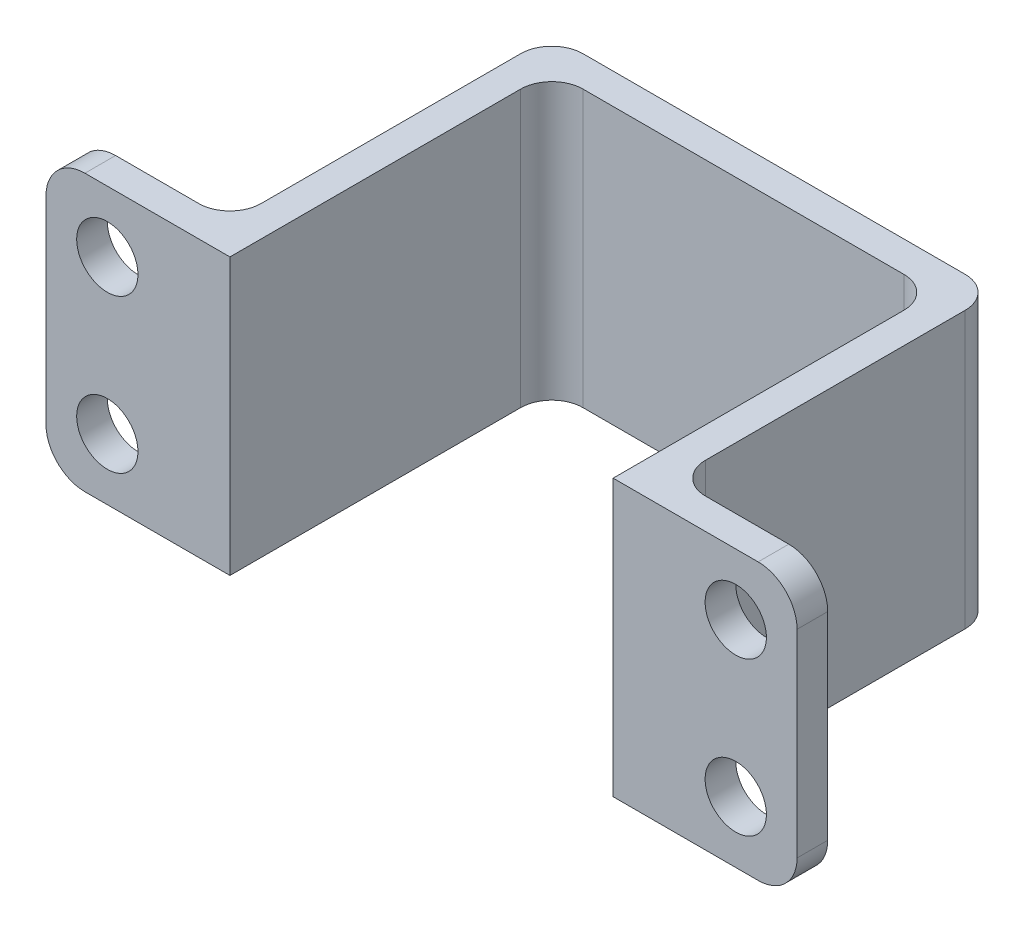
SolidWorks part; units mm, degrees
ref_plane "Front Plane" through (0, 0, 0) normal (0, 0, 1) x (1, 0, 0)
ref_plane "Top Plane" through (0, 0, 0) normal (0, 1, 0) x (1, 0, 0)
ref_plane "Right Plane" through (0, 0, 0) normal (1, 0, 0) x (0, 0, -1)
sketch "Sketch1" plane through (0, 0, 0) normal (0, 1, 0) x (1, 0, 0)
  line L0 (12.5, 0) -> (13.5, 0)
  line L2 (0, 0) -> (0, 9.484)
  line L3 (1.016, 10.5) -> (11.484, 10.5)
  line L4 (12.5, 0) -> (12.5, 9.484)
  line L5 (-1, 0) -> (0, 0)
  line L6 (-1, 2.016) -> (-1, 10.484)
  line L7 (0.016, 11.5) -> (12.484, 11.5)
  line L8 (13.5, 2.016) -> (13.5, 10.484)
  line L10 (-1, 0) -> (-6, 0)
  line L12 (-2.016, 1) -> (-6, 1)
  line L13 (-6, 0) -> (-6, 1)
  line L14 (13.5, 0) -> (18.5, 0)
  line L16 (14.516, 1) -> (18.5, 1)
  line L17 (18.5, 0) -> (18.5, 1)
  arc A0 (13.5, 2.016) -> (14.516, 1) centre (14.516, 2.016) ccw
  arc A1 (-1, 10.484) -> (0.016, 11.5) centre (0.016, 10.484) cw
  arc A2 (12.484, 11.5) -> (13.5, 10.484) centre (12.484, 10.484) cw
  arc A3 (11.484, 10.5) -> (12.5, 9.484) centre (11.484, 9.484) cw
  arc A4 (0, 9.484) -> (1.016, 10.5) centre (1.016, 9.484) cw
  arc A5 (-1, 2.016) -> (-2.016, 1) centre (-2.016, 2.016) cw
  point P23 (12.5, 10.5)
  point P26 (0, 10.5)
  dimension "D10" = 1.016
  dimension "D1" = 12.5
  dimension "D2" = 10.5
  dimension "D3" = 1
  dimension "D4" = 1
  dimension "D5" = 1
  dimension "D6" = 1
  dimension "D7" = 6
  dimension "D8" = 6
  dimension "D9" = 1
extrude "Boss-Extrude1" add sketch "Sketch1" along normal blind 9
sketch "Sketch2" plane through (0, 0, -1) normal (0, 0, -1) x (-1, 0, 0)
  line L0 (2.016, 0) -> (6, 0) construction
  line L1 (6, 9) -> (6, 0) construction
  line L2 (2.016, 9) -> (6, 9) construction
  line L3 (-18.5, 0) -> (-14.516, 0) construction
  line L4 (-18.5, 9) -> (-14.516, 9) construction
  line L5 (-18.5, 9) -> (-18.5, 0) construction
  circle A0 centre (4, 2) radius 1
  circle A1 centre (4, 7) radius 1
  circle A2 centre (-16.5, 2) radius 1
  circle A3 centre (-16.5, 7) radius 1
  dimension "D5" = 2
  dimension "D6" = 2
  dimension "D7" = 2
  dimension "D8" = 2
  dimension "D1" = 2
  dimension "D2" = 2
  dimension "D3" = 2
  dimension "D4" = 2
  dimension "D9" = 2
  dimension "D10" = 2
  dimension "D11" = 2
  dimension "D12" = 2
extrude "Cut-Extrude1" cut sketch "Sketch2" against normal through all
fillet "Fillet1" radius 1.27 4 edges at (-6, 0, -0.5) (-6, 9, -0.5) (18.5, 0, -0.5) (18.5, 9, -0.5)
